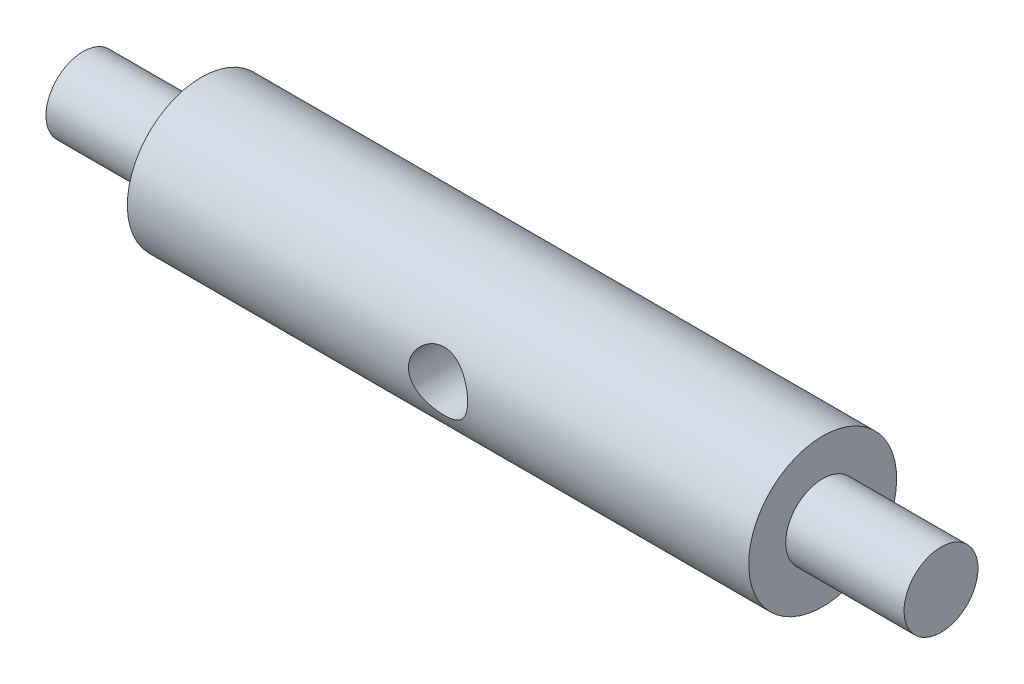
SolidWorks part; units mm, degrees
ref_plane "前基準面" through (0, 0, 0) normal (0, 0, 1) x (1, 0, 0)
ref_plane "上基準面" through (0, 0, 0) normal (0, 1, 0) x (1, 0, 0)
ref_plane "右基準面" through (0, 0, 0) normal (1, 0, 0) x (0, 0, -1)
sketch "草圖1" plane through (0, 0, 0) normal (0, 0, 1) x (1, 0, 0)
  line L0 (-29, 0) -> (-29, 2.5)
  line L1 (-29, 2.5) -> (-21, 2.5)
  line L2 (-21, 2.5) -> (-21, 5)
  line L3 (-21, 5) -> (21, 5)
  line L4 (21, 5) -> (21, 2.5)
  line L5 (21, 2.5) -> (29, 2.5)
  line L6 (29, 2.5) -> (29, 0)
  line L7 (29, 0) -> (-29, 0)
  dimension "D1" = 2.5
  dimension "D2" = 8
  dimension "D3" = 5
  dimension "D4" = 0
  dimension "D5" = 42
  dimension "D6" = 21
revolve "旋轉1" add sketch "草圖1" angle 360 about L7
sketch "草圖3" plane through (0, 0, 0) normal (0, 0, 1) x (1, 0, 0)
  circle A0 centre (0, 0) radius 2
  dimension "D1" = 4
extrude "除料-伸長1" cut sketch "草圖3" against normal mid plane 20
